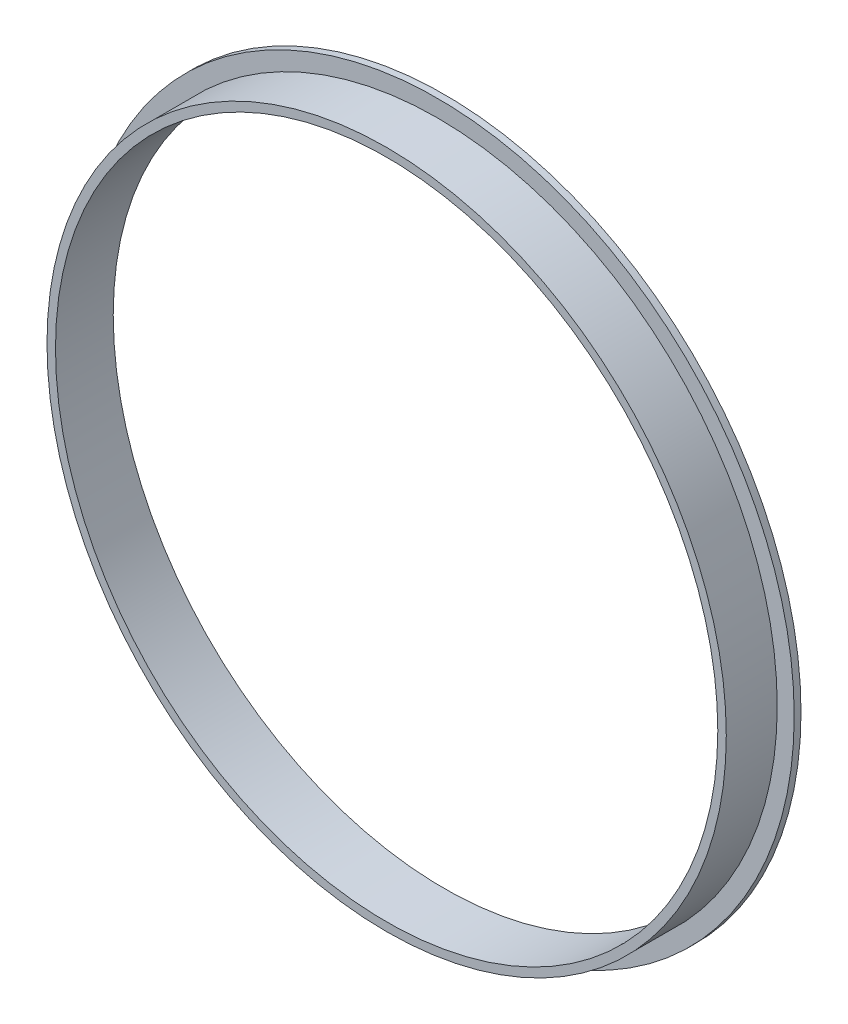
SolidWorks part; units mm, degrees
ref_plane "Alzado" through (0, 0, 0) normal (0, 0, 1) x (1, 0, 0)
ref_plane "Planta" through (0, 0, 0) normal (0, 1, 0) x (1, 0, 0)
ref_plane "Vista lateral" through (0, 0, 0) normal (1, 0, 0) x (0, 0, -1)
sketch "Croquis1" plane through (0, 0, 0) normal (0, 0, 1) x (1, 0, 0)
  circle A0 centre (0, 0) radius 21
  dimension "D1" = 42
extrude "Saliente-Extruir1" add sketch "Croquis1" along normal blind 0.4
sketch "Croquis2" plane through (0, 0, 0.4) normal (0, 0, 1) x (1, 0, 0)
  circle A0 centre (0, 0) radius 20
  dimension "D1" = 40
extrude "Saliente-Extruir2" add sketch "Croquis2" along normal blind 3
sketch "Croquis3" plane through (0, 0, 3.4) normal (0, 0, 1) x (1, 0, 0)
  circle A0 centre (0, 0) radius 19.5
  dimension "D1" = 39
extrude "Cortar-Extruir1" cut sketch "Croquis3" against normal through all
